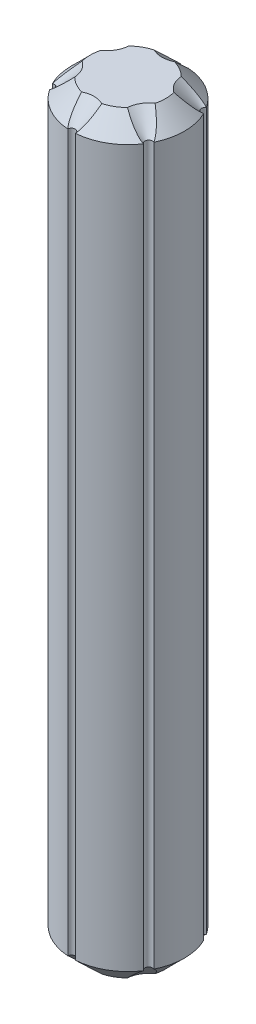
SolidWorks part; units mm, degrees
ref_plane "Front Plane" through (0, 0, 0) normal (0, 0, 1) x (1, 0, 0)
ref_plane "Top Plane" through (0, 0, 0) normal (0, 1, 0) x (1, 0, 0)
ref_plane "Right Plane" through (0, 0, 0) normal (1, 0, 0) x (0, 0, -1)
sketch "Sketch1" plane through (0, 0, 0) normal (0, 1, 0) x (1, 0, 0)
  circle A0 centre (0, 0) radius 3
  dimension "D1" = 6
extrude "Boss-Extrude1" add sketch "Sketch1" along normal blind 40
sketch "Sketch2" plane through (0, 40, 0) normal (0, 1, 0) x (1, 0, 0)
  circle A0 centre (0, 3) radius 0.2
  circle A1 centre (0, 0) radius 3 construction
  dimension "D1" = 0.4
extrude "Cut-Extrude1" cut sketch "Sketch2" against normal through all both and the other way through all
pattern_circular "CirPattern1" count 6 over 360 about axis through (0, 0, 0) along (0, 1, 0) of "Cut-Extrude1"
chamfer "Chamfer1" distance 1 angle 45 24 edges at (0, 0, -2.8) (-1.5, 0, -2.5981) (-2.4249, 0, -1.4) (-3, 0, 0) (-2.4249, 0, 1.4) (-1.5, 0, 2.5981) (0, 0, 2.8) (1.5, 0, 2.5981) (2.4249, 0, 1.4) (3, 0, 0) (2.4249, 0, -1.4) (1.5, 0, -2.5981) (1.5, 40, 2.5981) (3, 40, 0) (2.4249, 40, 1.4) (-1.5, 40, 2.5981) (0, 40, 2.8) (-3, 40, 0) (-2.4249, 40, 1.4) (-1.5, 40, -2.5981) (-2.4249, 40, -1.4) (0, 40, -2.8) (1.5, 40, -2.5981) (2.4249, 40, -1.4)
